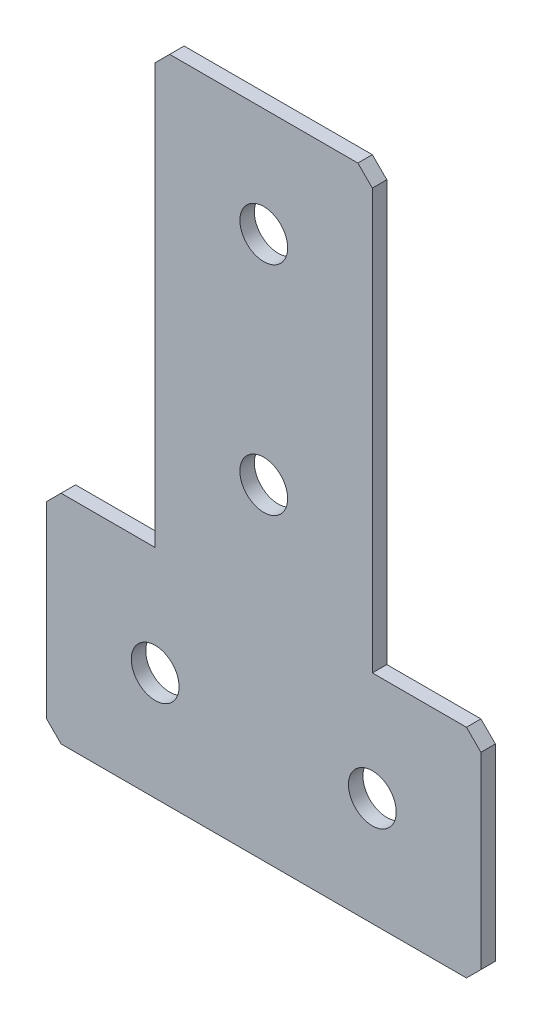
SolidWorks part; units mm, degrees
material "Простая углеродистая сталь"
ref_plane "Спереди(Плоскость XY)" through (0, 0, 0) normal (0, 0, 1) x (1, 0, 0)
ref_plane "Сверху(Плоскость XZ)" through (0, 0, 0) normal (0, 1, 0) x (1, 0, 0)
ref_plane "Справа(Плоскость ZY)" through (0, 0, 0) normal (1, 0, 0) x (0, 0, -1)
sketch "Эскиз1" plane through (0, 0, 0) normal (0, 0, -1) x (1, 0, 0)
  line L0 (0, 0) -> (0, 90) construction
  line L1 (-30, 90) -> (30, 90)
  line L2 (30, 90) -> (30, 60)
  line L3 (30, 60) -> (15, 60)
  line L4 (15, 60) -> (15, 0)
  line L5 (15, 0) -> (-15, 0)
  line L6 (-30, 90) -> (-30, 60)
  line L7 (-30, 60) -> (-15, 60)
  line L8 (-15, 60) -> (-15, 0)
  line L10 (-30, 75) -> (30, 75) construction
  dimension "D1" = 90
  dimension "D2" = 60
  dimension "D3" = 30
extrude "Бобышка-Вытянуть1" add sketch "Эскиз1" along normal blind 2
hole_wizard "Отверстие с зазором M61" positions "Эскиз2" profile "Эскиз3" hole size "M6" standard "DIN" end condition through all
sketch "Эскиз2" plane through (0, 0, -2) normal (0, 0, -1) x (1, 0, 0)
  line L6 (0, 0) -> (0, 75) construction
  line L9 (-15, 75) -> (15, 75) construction
  line L12 (30, 75) -> (15, 75) construction
  line L13 (30, 60) -> (30, 90) construction
  line L15 (-15, 0) -> (15, 0) construction
  point P40 (-15, 75)
  point P42 (15, 75)
  point P44 (0, 45)
  point P46 (0, 15)
  dimension "D1" = 30
  dimension "D2" = 15
  dimension "D3" = 30
sketch "Эскиз3" plane through (0, -15, -2) normal (1, 0, 0) x (0, 1, 0)
  line L0 (0, 0) -> (0, 2)
  line L1 (0, 2) -> (3.3, 2)
  line L2 (3.3, 2) -> (3.3, 0)
  line L5 (3.3, 0) -> (0, 0)
  line L11 (0, -6.35) -> (0, 107.95) construction
  dimension "Диаметр сквозного отверстия" = 6.6
  dimension "Глубина сквозного отверстия" = 2
chamfer "Фаска1" distance 2 angle 45 6 edges at (15, 0, -1) (30, -60, -1) (30, -90, -1) (-30, -90, -1) (-30, -60, -1) (-15, 0, -1)
